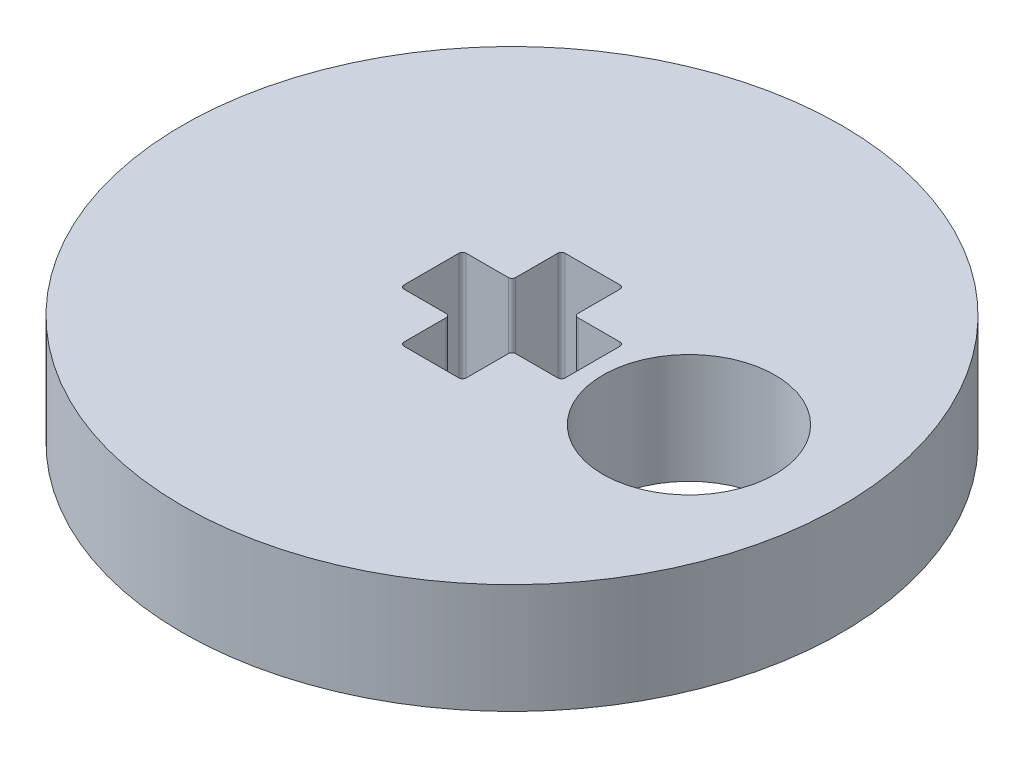
SolidWorks part; units mm, degrees
ref_plane "Front Plane" through (0, 0, 0) normal (0, 0, 1) x (1, 0, 0)
ref_plane "Top Plane" through (0, 0, 0) normal (0, 1, 0) x (1, 0, 0)
ref_plane "Right Plane" through (0, 0, 0) normal (1, 0, 0) x (0, 0, -1)
sketch "Sketch1" plane through (0, 0, 0) normal (0, 1, 0) x (1, 0, 0)
  line L6 (-2.2, 0.85) -> (-2.2, -0.85)
  line L7 (-2.2, -0.85) -> (-0.85, -0.85)
  line L8 (-0.85, -0.85) -> (-0.85, -2.2)
  line L9 (-0.85, -2.2) -> (0.85, -2.2)
  line L10 (0.85, -2.2) -> (0.85, -0.85)
  line L11 (0.85, -0.85) -> (2.2, -0.85)
  line L12 (2.2, -0.85) -> (2.2, 0.85)
  line L13 (2.2, 0.85) -> (0.85, 0.85)
  line L14 (0.85, 0.85) -> (0.85, 2.2)
  line L15 (0.85, 2.2) -> (-0.85, 2.2)
  line L16 (-0.85, 2.2) -> (-0.85, 0.85)
  line L17 (-0.85, 0.85) -> (-2.2, 0.85)
  circle A0 centre (0, 0) radius 9
  circle A1 centre (4.9973, -0.1648) radius 2.35
  circle A2 centre (0, 0) radius 2.3585 construction
  dimension "D1" = 18
  dimension "D3" = 4.7
  dimension "D2" = 4.9973
  dimension "D4" = 1.35
  dimension "D5" = 1.7
extrude "Boss-Extrude1" add sketch "Sketch1" along normal blind 3
fillet "Fillet1" radius 0.1 12 edges at (2.2, 1.5, 0.85) (0.85, 1.5, 0.85) (0.85, 1.5, 2.2) (-0.85, 1.5, 2.2) (-0.85, 1.5, 0.85) (-2.2, 1.5, 0.85) (2.2, 1.5, -0.85) (0.85, 1.5, -0.85) (0.85, 1.5, -2.2) (-0.85, 1.5, -2.2) (-0.85, 1.5, -0.85) (-2.2, 1.5, -0.85)
